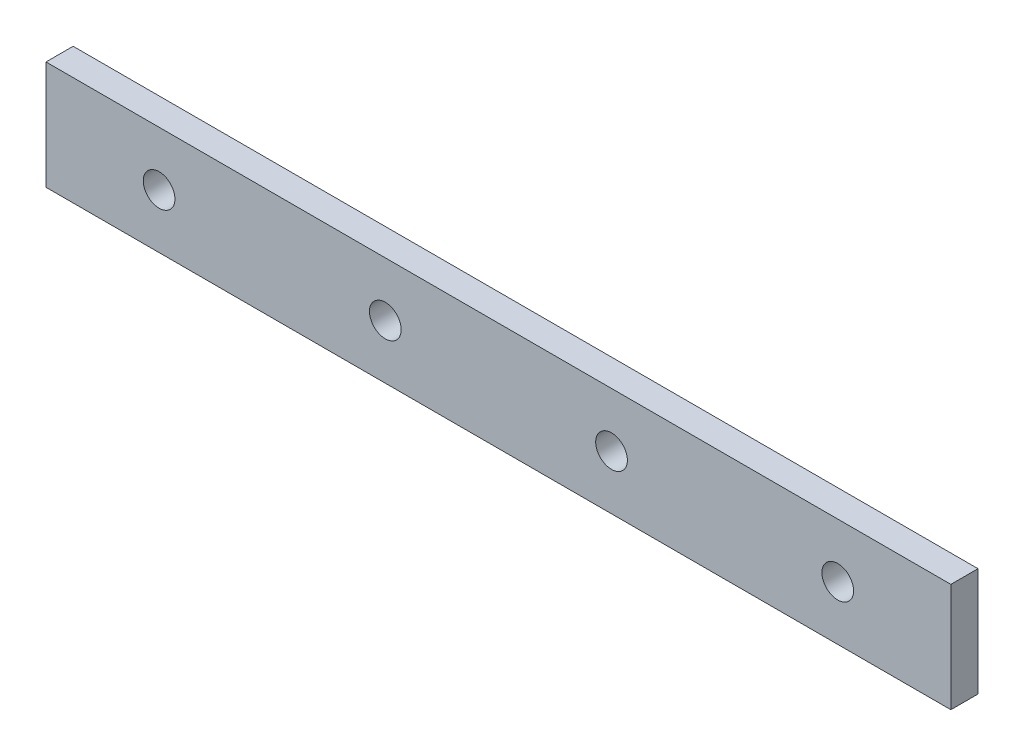
SolidWorks part; units mm, degrees
ref_plane "Front Plane" through (0, 0, 0) normal (0, 0, 1) x (1, 0, 0)
ref_plane "Top Plane" through (0, 0, 0) normal (0, 1, 0) x (1, 0, 0)
ref_plane "Right Plane" through (0, 0, 0) normal (1, 0, 0) x (0, 0, -1)
sketch "Sketch1" plane through (0, 0, 0) normal (0, 0, 1) x (1, 0, 0)
  line L1 (-50, -6) -> (50, -6)
  line L2 (-50, -6) -> (-50, 6)
  line L3 (-50, 6) -> (50, 6)
  line L4 (50, -6) -> (50, 6)
  line L5 (-50, -6) -> (50, 6) construction
  line L6 (-50, 6) -> (50, -6) construction
  point P0 (0, 0)
  dimension "D1" = 100
  dimension "D2" = 12
extrude "Boss-Extrude1" add sketch "Sketch1" along normal blind 3 contours L1 L4 L3 L2
sketch "Sketch7" plane through (0, 0, 3) normal (0, 0, 1) x (1, 0, 0)
  line L0 (50, -6) -> (50, 6) construction
  circle A0 centre (37.5, 0) radius 1.75
  point P5 (0, 0)
  dimension "D2" = 3.5
  dimension "D1" = 12.5
extrude "Cut-Extrude1" cut sketch "Sketch7" against normal through all
pattern_linear "LPattern1" count 4 spacing 25 along (-1, 0, 0) of "Cut-Extrude1"
